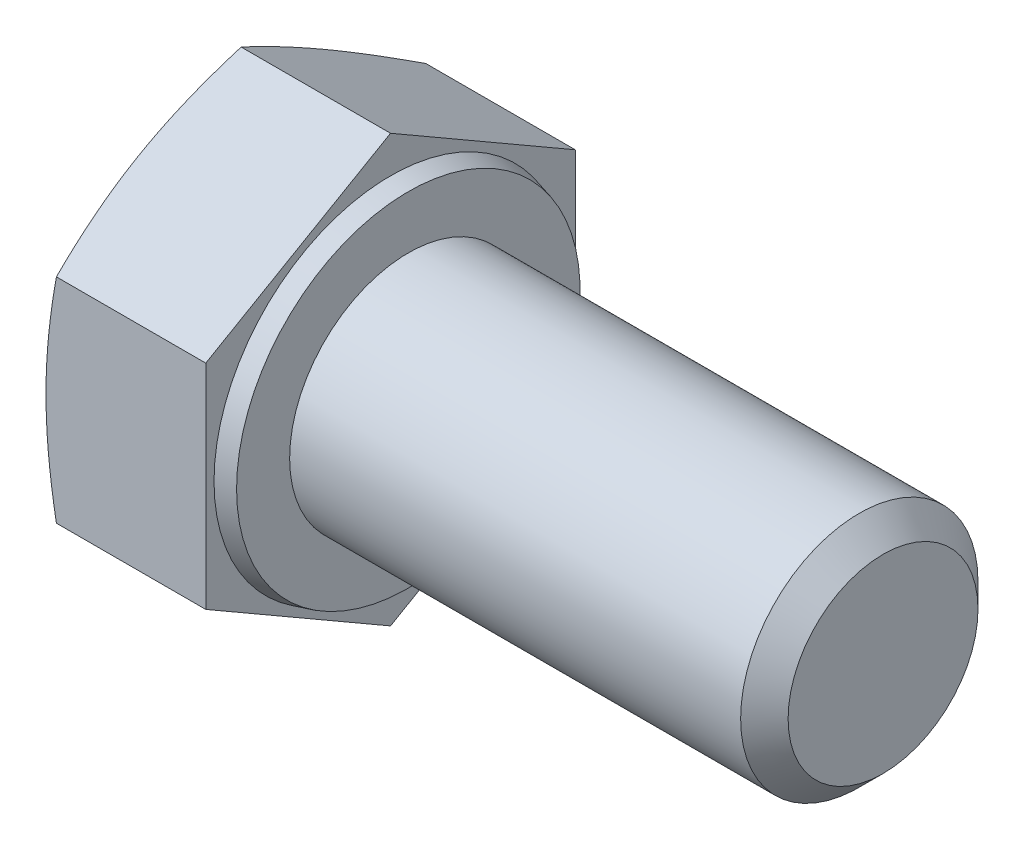
SolidWorks part; units mm, degrees
material "AISI 1020"
ref_plane "Спереди" through (0, 0, 0) normal (0, 0, 1) x (1, 0, 0)
ref_plane "Сверху" through (0, 0, 0) normal (0, 1, 0) x (1, 0, 0)
ref_plane "Справа" through (0, 0, 0) normal (1, 0, 0) x (0, 0, -1)
sketch "Эскиз1" plane through (0, 0, 0) normal (0, 0, 1) x (1, 0, 0)
  line L0 (-1000, 0) -> (49000, 0) construction
  line L1 (-5.45, 0) -> (-5.45, 7.19)
  line L2 (-5.45, 7.19) -> (0, 7.19)
  line L3 (0, 7.19) -> (0, 5.949)
  line L4 (0.6, 4) -> (16.6, 4)
  line L5 (16.6, 4) -> (16.6, 0)
  line L6 (-5.45, 0) -> (16.6, 0)
  line L7 (0, 5.949) -> (0.6, 5.7882)
  line L8 (0.6, 5.7882) -> (0.6, 4)
  line L9 (0.5, 0) -> (0.5, 5.815) construction
  dimension "_d" = 8
  dimension "D1" = 16
  dimension "D5" = 14.38
  dimension "D2" = 0.6
  dimension "D3" = 5.45
  dimension "D4" = 0.1
  dimension "D6" = 11.63
  dimension "D7" = 75
revolve "Повернуть1" add sketch "Эскиз1" angle 360 about L0
sketch "Эскиз2" plane through (-5.45, 0, 0) normal (-1, 0, 0) x (0, 0, 1)
  line L1 (0, -7.19) -> (6.2267, -3.595)
  line L2 (6.2267, -3.595) -> (6.2267, 3.595)
  line L3 (6.2267, 3.595) -> (0, 7.19)
  line L4 (0, 7.19) -> (-6.2267, 3.595)
  line L5 (-6.2267, 3.595) -> (-6.2267, -3.595)
  line L6 (-6.2267, -3.595) -> (0, -7.19)
  circle A0 centre (0, 0) radius 6.2267 construction
  circle A1 centre (0, 0) radius 7.19 construction
extrude "Вырез-Вытянуть1" cut sketch "Эскиз2" against normal through all flip side to cut
sketch "Эскиз4" plane through (0, 0, 0) normal (0, 0, 1) x (1, 0, 0)
  line L0 (-1000, 0) -> (49000, 0) construction
  line L1 (-5.45, 6.0468) -> (-5.0339, 7.19)
  line L2 (-5.0339, 7.19) -> (-5.45, 7.19)
  line L3 (-5.45, 7.19) -> (-5.45, 6.0468)
  line L4 (-5.45, 3.595) -> (-5.45, 7.19) construction
  line L6 (0, 7.19) -> (-5.45, 7.19) construction
  dimension "D1" = 20
  dimension "D2" = 12.0935
revolve "Вырез-Повернуть1" cut sketch "Эскиз4" angle 360 about L0
chamfer "Фаска1" distance 0.8 angle 45 1 edges at (16.6, 0, 4)
equation "\"l\"= 16'длина болта"
equation "\"_d\"= 8'диаметр болта"
equation "\"b\"= 20'длина резьбы"
equation "\"k\"= 5.45'толщина шляпки"
equation "\"e\"= 14.38'диаметр головки описанный"
equation "\"S\"= 12.73'размер под ключ"
equation "\"_d@Эскиз1\"=\"_d\""
equation "\"dw\"= 11.63"
equation "\"da\"= 9.78"
equation "\"с\"= 0.6"
equation "\"D1@Эскиз1\"=\"l\""
equation "\"D5@Эскиз1\"=\"e\""
equation "\"D2@Эскиз1\"=\"с\""
equation "\"D3@Эскиз1\"=\"k\""
equation "\"D2@Эскиз4\"=\"S\"*0.95"
equation "\"D1@Фаска1\"=\"_d\"/10"
equation "\"D6@Эскиз1\"=\"dw\""
